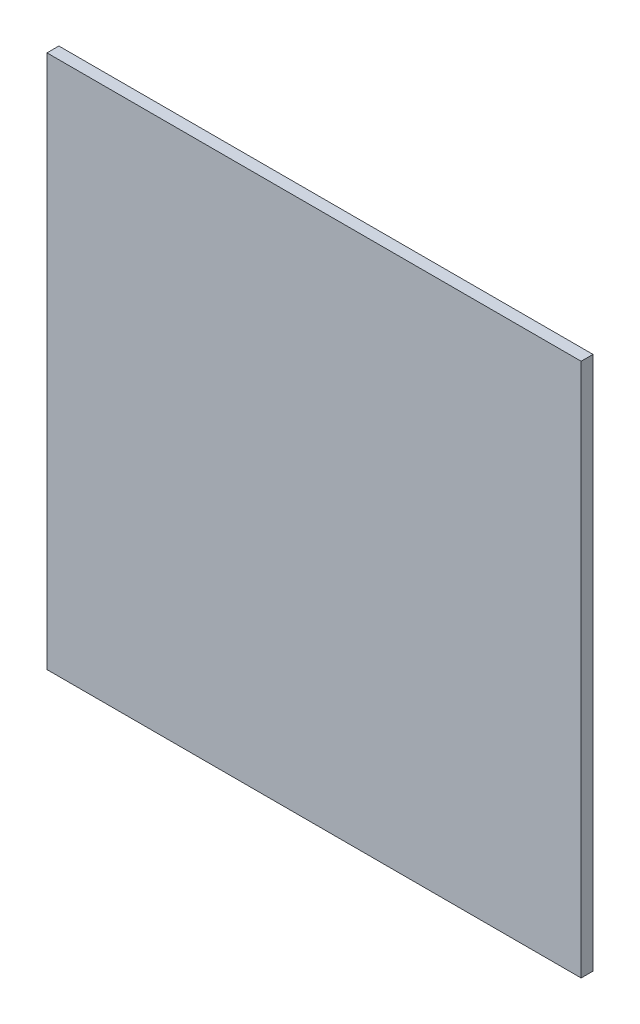
SolidWorks part; units mm, degrees
ref_plane "Front Plane" through (0, 0, 0) normal (0, 0, 1) x (1, 0, 0)
ref_plane "Top Plane" through (0, 0, 0) normal (0, 1, 0) x (1, 0, 0)
ref_plane "Right Plane" through (0, 0, 0) normal (1, 0, 0) x (0, 0, -1)
sketch "Sketch1" plane through (0, 0, 0) normal (0, 0, 1) x (1, 0, 0)
  line L1 (-22.5, 22.5) -> (22.5, 22.5)
  line L2 (-22.5, 22.5) -> (-22.5, -22.5)
  line L3 (-22.5, -22.5) -> (22.5, -22.5)
  line L4 (22.5, 22.5) -> (22.5, -22.5)
  line L5 (-22.5, 22.5) -> (22.5, -22.5) construction
  line L6 (-22.5, -22.5) -> (22.5, 22.5) construction
  point P0 (0, 0)
  dimension "D1" = 45
  dimension "D2" = 45
extrude "Boss-Extrude1" add sketch "Sketch1" along normal blind 1
sketch "Sketch3" plane through (22.5, 0, 0) normal (1, 0, 0) x (0, 0, -1)
  line L0 (-1, -22.5) -> (-1, 22.5) construction
  point P0 (-1, 0)
